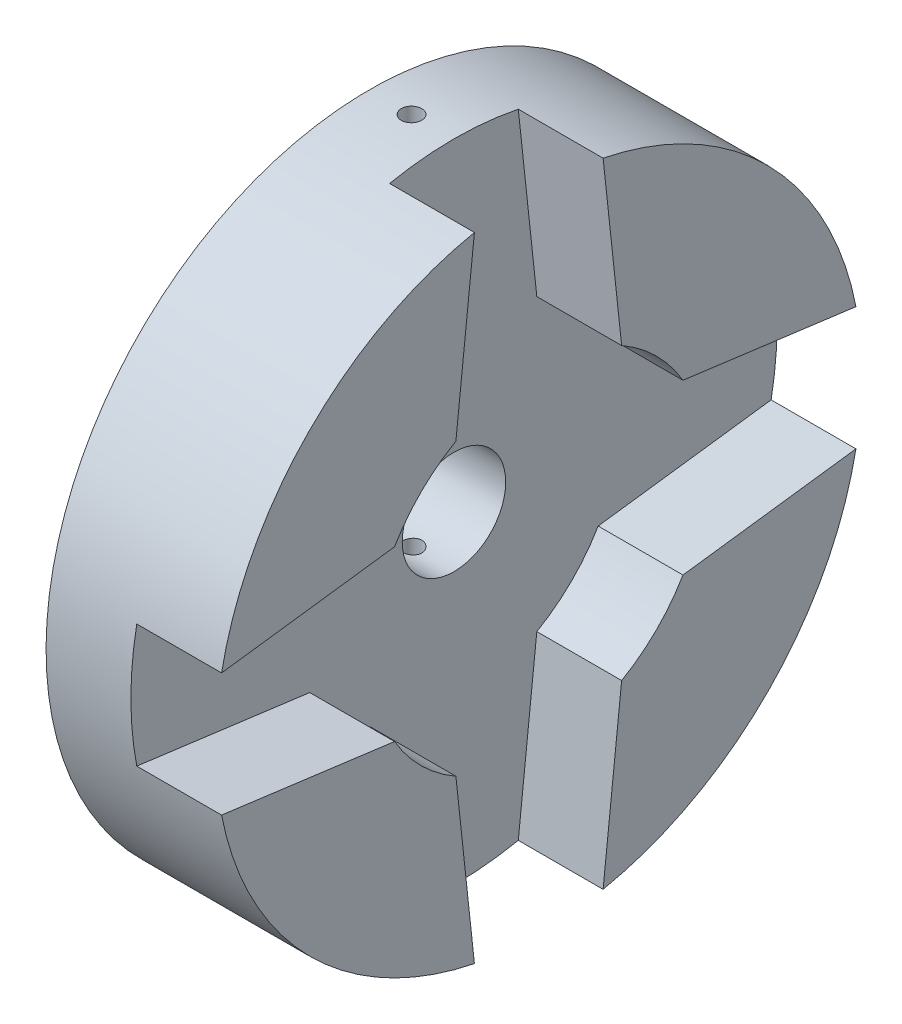
SolidWorks part; units mm, degrees
ref_plane "Front Plane" through (0, 0, 0) normal (0, 0, 1) x (1, 0, 0)
ref_plane "Top Plane" through (0, 0, 0) normal (0, 1, 0) x (1, 0, 0)
ref_plane "Right Plane" through (0, 0, 0) normal (1, 0, 0) x (0, 0, -1)
sketch "Reference" plane through (0, 0, 0) normal (1, 0, 0) x (0, 0, -1)
  line L0 (-26.48, 0) -> (26.48, 0) construction
  line L1 (0, 29.015) -> (0, -29.015) construction
  line L2 (-4.945, 8.0118) -> (4.945, 8.0118) construction
  line L3 (7.9335, 5.0471) -> (7.9335, -5.0471) construction
  line L4 (4.945, -8.0118) -> (-4.945, -8.0118) construction
  line L5 (-7.9335, -5.0471) -> (-7.9335, 5.0471) construction
  line L6 (-3, 26.015) -> (-4.945, 8.0118) construction
  line L7 (3, 26.015) -> (4.945, 8.0118) construction
  line L8 (-23.48, 3) -> (-7.9335, 5.0471) construction
  line L9 (-23.48, -3) -> (-7.9335, -5.0471) construction
  line L10 (3, -26.015) -> (4.945, -8.0118) construction
  line L11 (-3, -26.015) -> (-4.945, -8.0118) construction
  line L12 (23.48, -3) -> (7.9335, -5.0471) construction
  line L13 (23.48, 3) -> (7.9335, 5.0471) construction
  circle A0 centre (0, 0) radius 9.415 construction
  circle A1 centre (0, 0) radius 9.4028 construction
  arc A2 (3, 26.015) -> (-3, 26.015) centre (0, 26.015) ccw construction
  arc A3 (-23.48, 3) -> (-23.48, -3) centre (-23.48, 0) ccw construction
  arc A4 (3, -26.015) -> (-3, -26.015) centre (0, -26.015) cw construction
  arc A5 (23.48, 3) -> (23.48, -3) centre (23.48, 0) cw construction
  arc A6 (-7.9335, -5.0471) -> (-4.945, -8.0118) centre (-0.063, -0.1021) ccw construction
  arc A7 (4.945, -8.0118) -> (7.9335, -5.0471) centre (0.063, -0.1021) ccw construction
  arc A8 (7.9335, 5.0471) -> (4.945, 8.0118) centre (0.063, 0.1021) ccw construction
  arc A9 (-7.9335, 5.0471) -> (-4.945, 8.0118) centre (-0.063, 0.1021) cw construction
  point P5 (0, 0)
  point P8 (0, 0)
  point P11 (0, 8.0118)
  point P14 (-7.8403, 0)
  point P22 (0, 0)
sketch "Sketch2" plane through (0, 0, 0) normal (1, 0, 0) x (0, 0, -1)
  line L0 (0, 29.015) -> (0, -29.015) construction
  circle A0 centre (0, 0) radius 19.05
  dimension "D1" = 38.1
extrude "Boss-Extrude1" add sketch "Sketch2" along normal blind 5 contours A0
sketch "Sketch4" plane through (5, 0, 0) normal (1, 0, 0) x (0, 0, -1)
  line L1 (4.8866, 8.5524) -> (3.7937, 18.6684)
  line L10 (-3, 26.015) -> (-4.945, 8.0118) construction
  line L11 (3, 26.015) -> (4.945, 8.0118) construction
  line L12 (-4.8866, 8.5524) -> (-3.7937, 18.6684)
  line L13 (-23.48, 3) -> (-7.9335, 5.0471) construction
  line L14 (-8.503, 4.9721) -> (-18.7011, 3.6293)
  line L15 (23.48, 3) -> (7.9335, 5.0471) construction
  line L16 (23.48, -3) -> (7.9335, -5.0471) construction
  line L17 (3, -26.015) -> (4.945, -8.0118) construction
  line L18 (-3, -26.015) -> (-4.945, -8.0118) construction
  line L19 (-23.48, -3) -> (-7.9335, -5.0471) construction
  line L20 (-8.503, -4.9721) -> (-18.7011, -3.6293)
  line L21 (-4.8866, -8.5524) -> (-3.7937, -18.6684)
  line L22 (4.8866, -8.5524) -> (3.7937, -18.6684)
  line L23 (8.503, -4.9721) -> (18.7011, -3.6293)
  line L24 (8.503, 4.9721) -> (18.7011, 3.6293)
  arc A1 (-3.7937, 18.6684) -> (-18.7011, 3.6293) centre (0, 0) ccw
  circle A10 centre (0, 0) radius 19.05 construction
  circle A11 centre (0, 0) radius 9.85 construction
  arc A12 (3.7937, 18.6684) -> (18.7011, 3.6293) centre (0, 0) cw
  arc A13 (3.7937, -18.6684) -> (18.7011, -3.6293) centre (0, 0) ccw
  arc A14 (-3.7937, -18.6684) -> (-18.7011, -3.6293) centre (0, 0) cw
  arc A15 (-8.503, -4.9721) -> (-4.8866, -8.5524) centre (0, 0) ccw
  arc A16 (4.8866, -8.5524) -> (8.503, -4.9721) centre (0, 0) ccw
  arc A17 (8.503, 4.9721) -> (4.8866, 8.5524) centre (0, 0) ccw
  arc A18 (-4.8866, 8.5524) -> (-8.503, 4.9721) centre (0, 0) ccw
  point P4 (-4.8866, 8.5524)
  point P5 (-8.503, 4.9721)
  point P8 (4.8866, 8.5524)
  point P13 (8.503, 4.9721)
  point P18 (8.503, -4.9721)
  point P19 (4.8866, -8.5524)
  point P20 (-4.8866, -8.5524)
  point P21 (-8.503, -4.9721)
  dimension "D1" = 19.7
extrude "Boss-Extrude2" add sketch "Sketch4" along normal blind 5
sketch "Sketch6" plane through (0, 0, 0) normal (-1, 0, 0) x (0, 0, 1)
  line L0 (0, 29.015) -> (0, -29.015) construction
  circle A0 centre (0, 0) radius 3.05
  dimension "D1" = 6.1
extrude "Cut-Extrude1" cut sketch "Sketch6" against normal blind 25
sketch "Sketch5" plane through (0, 0, 0) normal (-1, 0, 0) x (0, 0, 1)
  line L0 (26.48, 0) -> (-26.48, 0) construction
  circle A0 centre (0, 0) radius 3
  dimension "D1" = 6
extrude "Boss-Extrude3" [suppressed] add sketch "Sketch5" along normal blind 25
sketch "Sketch7" [suppressed] plane through (0, 0, 0) normal (0, 1, 0) x (1, 0, 0)
  line L1 (-25, 3) -> (-25, -3) construction
  line L3 (-5.5, 0) -> (5.5, 0) construction
  circle A0 centre (-16.6, 0) radius 0.55
  point P2 (-16.6, -0.7154)
  point P3 (0, 0)
  point P6 (-16.6, 0)
  point P7 (-16.6, 0)
  dimension "D1" = 1.1
  dimension "D2" = 8.4
extrude "Cut-Extrude3" [suppressed] cut sketch "Sketch7" against normal mid plane 10
sketch "Sketch8" plane through (0, 0, 0) normal (0, 1, 0) x (1, 0, 0)
  line L0 (-5.5, 0) -> (5.5, 0) construction
  line L3 (0, -3) -> (0, 3) construction
  circle A0 centre (2.5, 0) radius 0.6
  dimension "D1" = 1.2
  dimension "D2" = 2.5
extrude "Cut-Extrude4" cut sketch "Sketch8" against normal mid plane 50 contours A0
